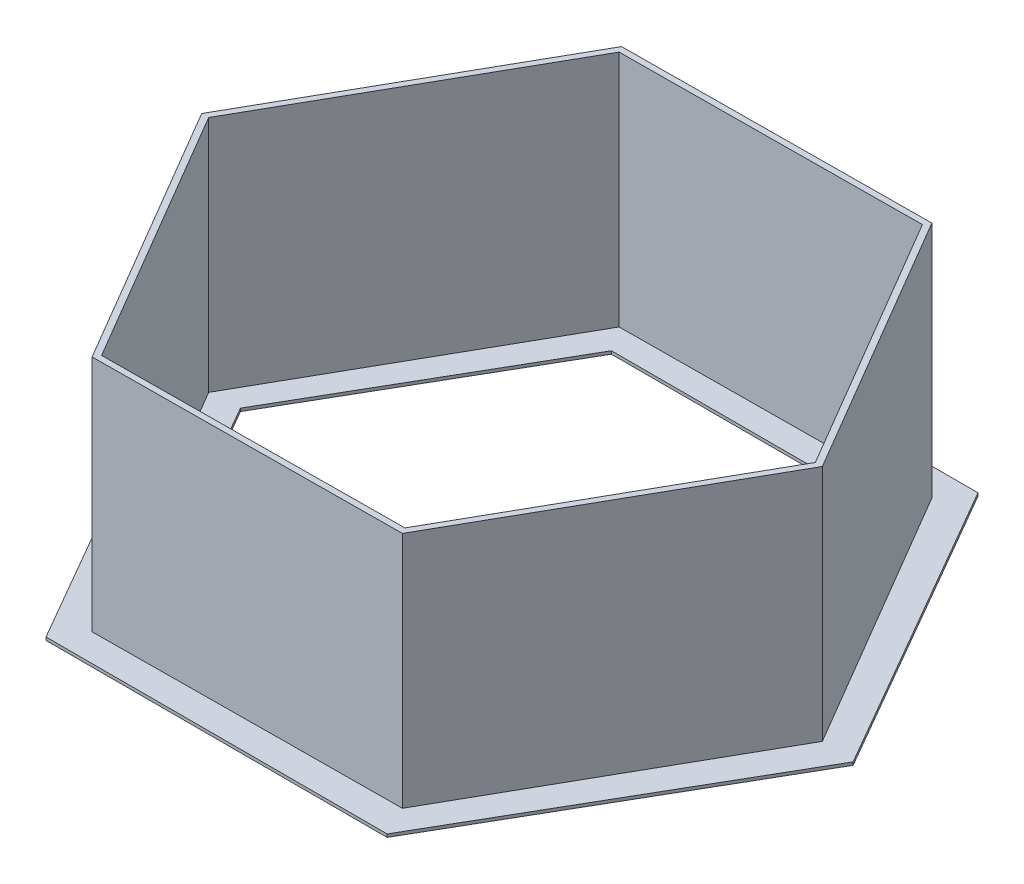
SolidWorks part; units mm, degrees
material "ASTM A36 Steel"
ref_plane "Front Plane" through (0, 0, 0) normal (0, 0, 1) x (1, 0, 0)
ref_plane "Top Plane" through (0, 0, 0) normal (0, 1, 0) x (1, 0, 0)
ref_plane "Right Plane" through (0, 0, 0) normal (1, 0, 0) x (0, 0, -1)
sketch "Sketch1" plane through (0, 0, 0) normal (0, 1, 0) x (1, 0, 0)
  line L1 (143.7695, -249.0161) -> (287.539, 0)
  line L2 (287.539, 0) -> (143.7695, 249.0161)
  line L3 (143.7695, 249.0161) -> (-143.7695, 249.0161)
  line L4 (-143.7695, 249.0161) -> (-287.539, 0)
  line L5 (-287.539, 0) -> (-143.7695, -249.0161)
  line L6 (-143.7695, -249.0161) -> (143.7695, -249.0161)
  line L7 (114.4401, -198.2161) -> (228.8802, 0)
  line L8 (228.8802, 0) -> (114.4401, 198.2161)
  line L9 (114.4401, 198.2161) -> (-114.4401, 198.2161)
  line L10 (-114.4401, 198.2161) -> (-228.8802, 0)
  line L11 (-228.8802, 0) -> (-114.4401, -198.2161)
  line L12 (-114.4401, -198.2161) -> (114.4401, -198.2161)
  dimension "D1" = 50.8
extrude "Boss-Extrude1" add sketch "Sketch1" along normal blind 2.54
sketch "Sketch2" plane through (0, 0, 0) normal (0, 1, 0) x (1, 0, 0)
  line L7 (128.1107, 225.8192) -> (-131.5098, 223.8567)
  line L8 (-131.5098, 223.8567) -> (-259.6205, -1.9624)
  line L9 (-259.6205, -1.9624) -> (-128.1107, -225.8192)
  line L10 (-128.1107, -225.8192) -> (131.5098, -223.8567)
  line L11 (131.5098, -223.8567) -> (259.6205, 1.9624)
  line L12 (259.6205, 1.9624) -> (128.1107, 225.8192)
  line L13 (125.2163, 220.7172) -> (-128.5385, 218.7991)
  line L14 (-128.5385, 218.7991) -> (-253.7548, -1.9181)
  line L15 (-253.7548, -1.9181) -> (-125.2163, -220.7172)
  line L16 (-125.2163, -220.7172) -> (128.5385, -218.7991)
  line L17 (128.5385, -218.7991) -> (253.7548, 1.9181)
  line L18 (253.7548, 1.9181) -> (125.2163, 220.7172)
extrude "Boss-Extrude2" add sketch "Sketch2" along normal blind 203.2
